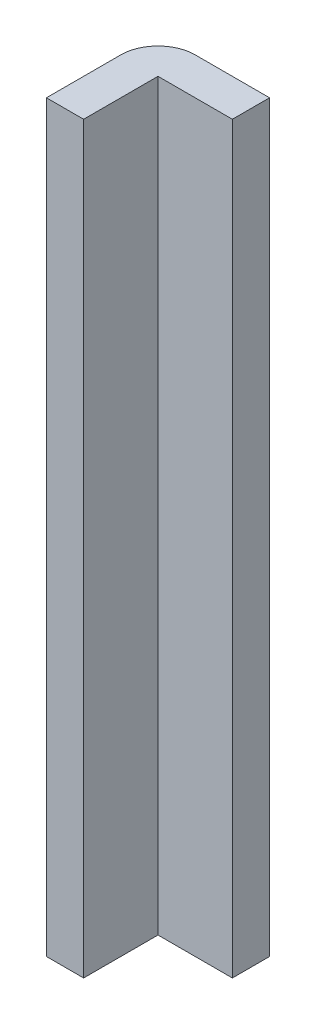
SolidWorks part; units mm, degrees
ref_plane "Front Plane" through (0, 0, 0) normal (0, 0, 1) x (1, 0, 0)
ref_plane "Top Plane" through (0, 0, 0) normal (0, 1, 0) x (1, 0, 0)
ref_plane "Right Plane" through (0, 0, 0) normal (1, 0, 0) x (0, 0, -1)
sketch "Sketch1" plane through (0, 0, 0) normal (0, 1, 0) x (1, 0, 0)
  line L1 (0, 0) -> (-2, 0)
  line L2 (0, 0) -> (0, 0.8896)
  line L4 (-2, 0) -> (-2, 6)
  line L7 (-2, 6) -> (4, 6)
  line L8 (0, 0.8896) -> (0, 4)
  line L9 (0, 4) -> (4, 4)
  line L10 (4, 6) -> (4, 4)
  point P0 (0, 0)
  point P9 (0, 0)
  point P10 (0, 1.3668)
  dimension "D1" = 6
  dimension "D2" = 6
  dimension "D3" = 2
  dimension "D4" = 2
extrude "Boss-Extrude1" add sketch "Sketch1" along normal blind 40
fillet "Fillet1" radius 2 1 edges at (-2, 20, -6)
equation "\"L\"=6"
equation "\"D1@Sketch1\"=\"L\""
equation "\"D2@Sketch1\"=\"L\""
equation "\"F\"=2"
equation "\"D1@Fillet1\"=\"F\""
